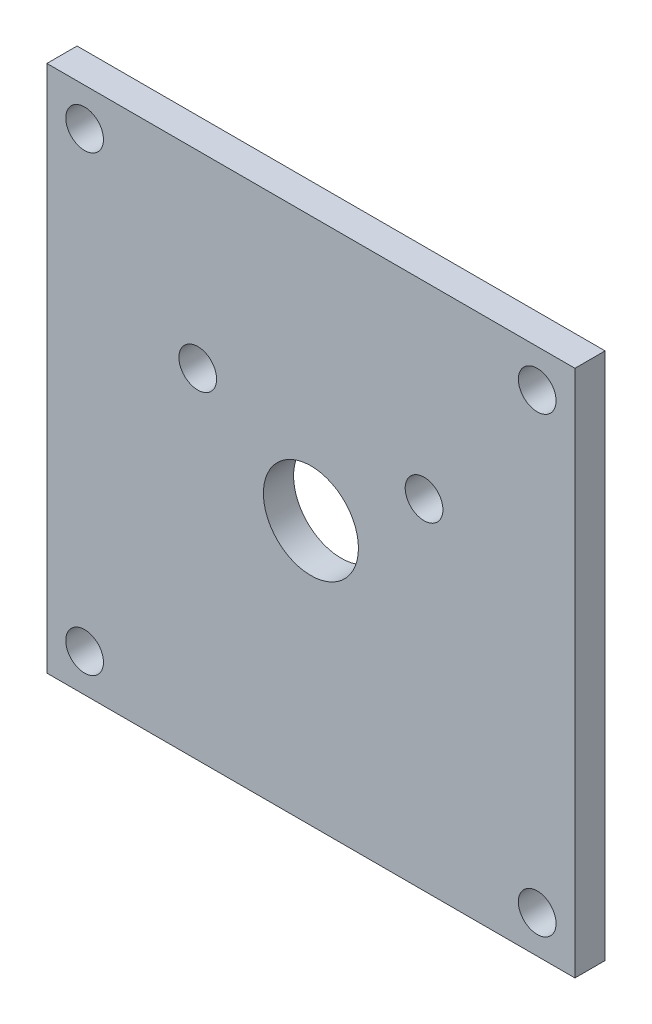
SolidWorks part; units mm, degrees
ref_plane "Front Plane" through (0, 0, 0) normal (0, 0, 1) x (1, 0, 0)
ref_plane "Top Plane" through (0, 0, 0) normal (0, 1, 0) x (1, 0, 0)
ref_plane "Right Plane" through (0, 0, 0) normal (1, 0, 0) x (0, 0, -1)
sketch "Sketch1" plane through (0, 0, 0) normal (0, 0, 1) x (1, 0, 0)
  line L1 (0, 0) -> (88.9, 0)
  line L2 (0, 0) -> (0, 88.9)
  line L3 (0, 88.9) -> (88.9, 88.9)
  line L4 (88.9, 0) -> (88.9, 88.9)
  dimension "D1" = 88.9
  dimension "D2" = 88.9
extrude "Boss-Extrude1" add sketch "Sketch1" along normal mid plane 5.08
sketch "Sketch2" plane through (0, 0, 2.54) normal (0, 0, 1) x (1, 0, 0)
  line L0 (44.45, 88.9) -> (44.45, 0) construction
  line L1 (82.55, 6.35) -> (6.35, 6.35) construction
  line L2 (82.55, 6.35) -> (82.55, 82.55) construction
  line L3 (82.55, 82.55) -> (6.35, 82.55) construction
  line L4 (6.35, 6.35) -> (6.35, 82.55) construction
  line L5 (82.55, 6.35) -> (6.35, 82.55) construction
  line L6 (82.55, 82.55) -> (6.35, 6.35) construction
  line L7 (88.9, 88.9) -> (0, 88.9) construction
  line L8 (0, 0) -> (88.9, 0) construction
  line L9 (25.4, 57.15) -> (63.5, 57.15) construction
  circle A0 centre (6.35, 82.55) radius 3.175
  circle A1 centre (82.55, 82.55) radius 3.175
  circle A2 centre (82.55, 6.35) radius 3.175
  circle A3 centre (6.35, 6.35) radius 3.175
  circle A4 centre (44.45, 44.45) radius 8.001
  circle A5 centre (25.4, 57.15) radius 3.175
  circle A6 centre (63.5, 57.15) radius 3.175
  point P0 (44.45, 44.45)
  point P12 (44.45, 44.45)
  point P22 (44.45, 57.15)
  dimension "D2" = 6.35
  dimension "D3" = 16.002
  dimension "D4" = 6.35
  dimension "D1" = 76.2
  dimension "D5" = 38.1
  dimension "D6" = 12.7
extrude "Cut-Extrude1" cut sketch "Sketch2" against normal through all
